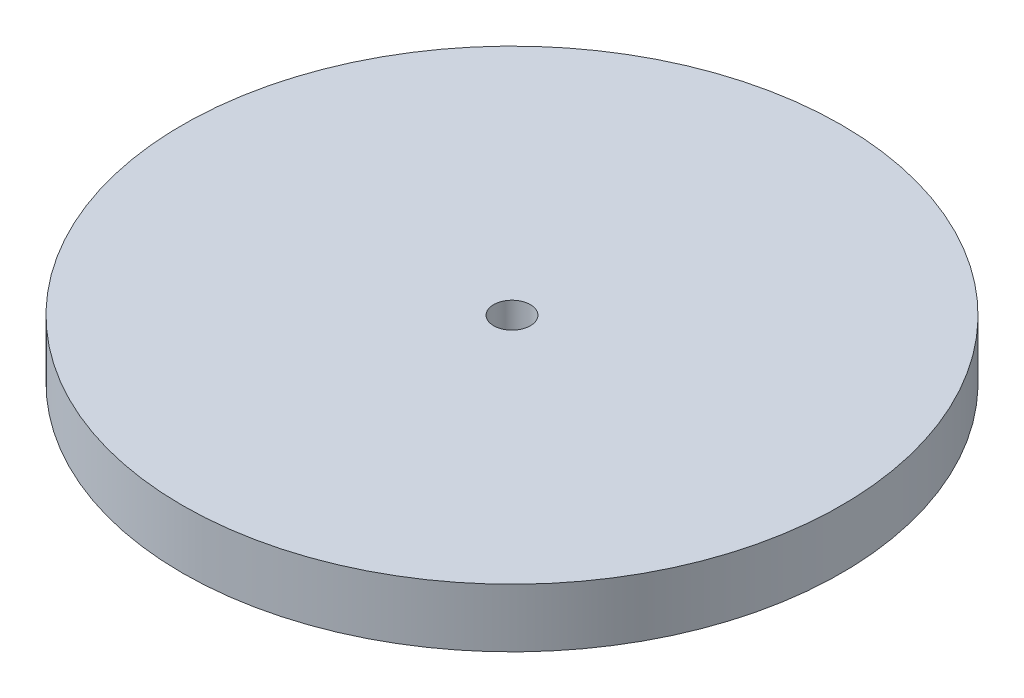
SolidWorks part; units mm, degrees
material "ABS"
ref_plane "Front Plane" through (0, 0, 0) normal (0, 0, 1) x (1, 0, 0)
ref_plane "Top Plane" through (0, 0, 0) normal (0, 1, 0) x (1, 0, 0)
ref_plane "Right Plane" through (0, 0, 0) normal (1, 0, 0) x (0, 0, -1)
sketch "Sketch1" plane through (0, 0, 0) normal (0, 1, 0) x (1, 0, 0)
  circle A0 centre (0, 0) radius 18
  dimension "D1" = 36
extrude "Boss-Extrude1" add sketch "Sketch1" along normal blind 3.2
sketch "Sketch2" plane through (0, 3.2, 0) normal (0, 1, 0) x (1, 0, 0)
  circle A0 centre (0, 0) radius 1.0025
  dimension "D1" = 2.005
extrude "Cut-Extrude1" cut sketch "Sketch2" against normal through all
